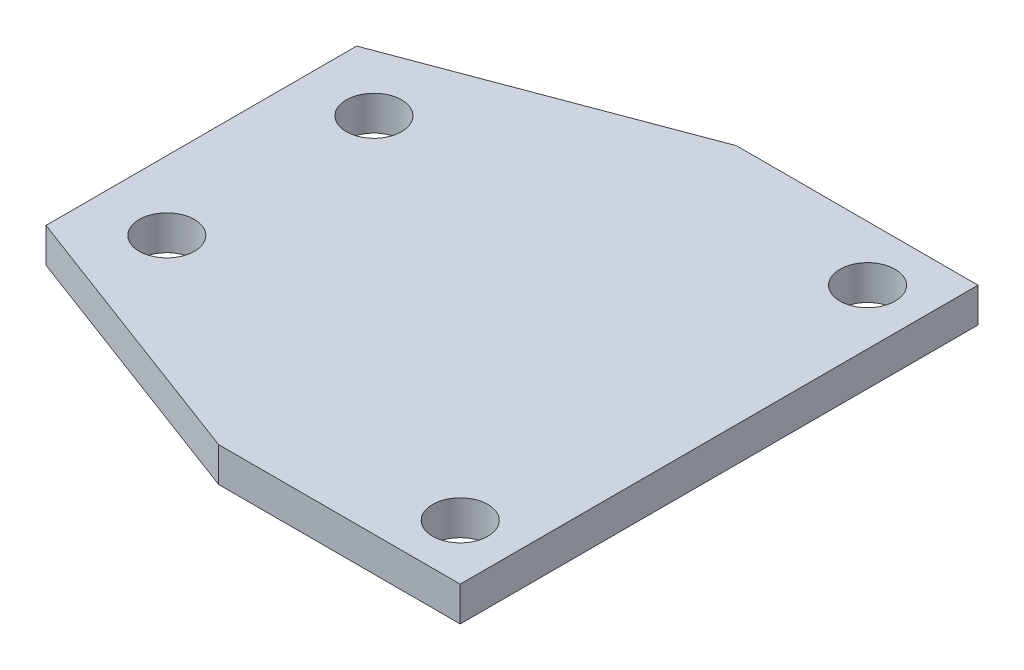
SolidWorks part; units mm, degrees
ref_plane "Front Plane" through (0, 0, 0) normal (0, 0, 1) x (1, 0, 0)
ref_plane "Top Plane" through (0, 0, 0) normal (0, 1, 0) x (1, 0, 0)
ref_plane "Right Plane" through (0, 0, 0) normal (1, 0, 0) x (0, 0, -1)
sketch "Sketch1" plane through (0, 0, 0) normal (0, 1, 0) x (1, 0, 0)
  line L1 (0, 0) -> (150, 0)
  line L2 (0, 0) -> (0, 150)
  line L3 (0, 150) -> (150, 150)
  line L4 (150, 0) -> (150, 150)
  dimension "D1" = 150
extrude "Boss-Extrude1" add sketch "Sketch1" along normal blind 10
chamfer "Chamfer1" distance 30 distance2 80 1 edges at (0, 5, 0)
chamfer "Chamfer2" distance 80 distance2 30 1 edges at (0, 5, -150)
sketch "Sketch2" plane through (0, 10, 0) normal (0, 1, 0) x (1, 0, 0)
  line L0 (150, 150) -> (80, 150) construction
  line L1 (150, 0) -> (150, 150) construction
  line L2 (80, 0) -> (150, 0) construction
  circle A0 centre (134, 134) radius 8
  circle A1 centre (134, 16) radius 8
  circle A2 centre (20, 105) radius 8
  circle A3 centre (20, 45) radius 8
  dimension "D1" = 16
  dimension "D2" = 16
  dimension "D3" = 16
  dimension "D4" = 16
  dimension "D5" = 16
  dimension "D6" = 16
  dimension "D7" = 16
  dimension "D8" = 16
  dimension "D9" = 130
  dimension "D10" = 130
  dimension "D11" = 45
  dimension "D12" = 45
extrude "Cut-Extrude1" cut sketch "Sketch2" against normal blind 10
